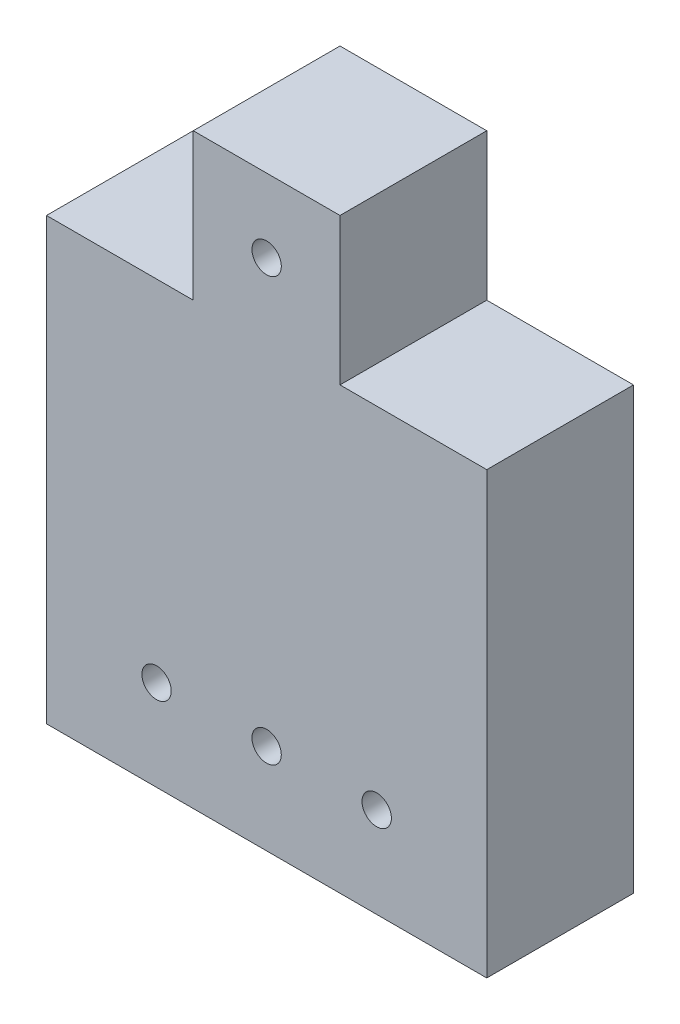
SolidWorks part; units mm, degrees
ref_plane "Front Plane" through (0, 0, 0) normal (0, 0, 1) x (1, 0, 0)
ref_plane "Top Plane" through (0, 0, 0) normal (0, 1, 0) x (1, 0, 0)
ref_plane "Right Plane" through (0, 0, 0) normal (1, 0, 0) x (0, 0, -1)
sketch "Sketch1" plane through (0, 0, 0) normal (0, 0, 1) x (1, 0, 0)
  line L1 (0, 0) -> (19.05, 0)
  line L2 (0, 0) -> (0, 25.4)
  line L3 (0, 25.4) -> (19.05, 25.4)
  line L4 (19.05, 0) -> (19.05, 25.4)
  dimension "D1" = 19.05
  dimension "D2" = 25.4
extrude "Boss-Extrude1" add sketch "Sketch1" along normal blind 6.35
sketch "Sketch2" plane through (0, 0, 0) normal (0, 0, -1) x (-1, 0, 0)
  line L1 (0, 25.4) -> (-6.35, 25.4)
  line L2 (0, 25.4) -> (0, 19.05)
  line L3 (0, 19.05) -> (-6.35, 19.05)
  line L4 (-6.35, 25.4) -> (-6.35, 19.05)
  dimension "D1" = 6.35
  dimension "D2" = 6.35
extrude "Cut-Extrude1" cut sketch "Sketch2" against normal through all
sketch "Sketch3" plane through (0, 0, 0) normal (0, 0, -1) x (-1, 0, 0)
  line L1 (-19.05, 25.4) -> (-12.7, 25.4)
  line L2 (-19.05, 25.4) -> (-19.05, 19.05)
  line L3 (-19.05, 19.05) -> (-12.7, 19.05)
  line L4 (-12.7, 25.4) -> (-12.7, 19.05)
  dimension "D1" = 6.35
  dimension "D2" = 6.35
extrude "Cut-Extrude2" cut sketch "Sketch3" against normal through all
sketch "Sketch4" plane through (0, 0, 0) normal (0, 0, -1) x (-1, 0, 0)
  line L0 (-9.525, 22.225) -> (-9.525, 19.05) construction
  line L1 (-9.525, 22.225) -> (-6.35, 22.225) construction
  line L4 (-6.35, 25.4) -> (-12.7, 25.4)
  line L5 (-12.7, 25.4) -> (-12.7, 19.05)
  line L6 (-12.7, 19.05) -> (-6.35, 19.05)
  line L7 (-6.35, 19.05) -> (-6.35, 25.4)
  line L8 (-6.35, 25.4) -> (-12.7, 25.4) construction
  line L9 (-12.7, 25.4) -> (-12.7, 19.05) construction
  line L10 (-12.7, 19.05) -> (-6.35, 19.05) construction
  line L11 (-6.35, 19.05) -> (-6.35, 25.4) construction
  circle A0 centre (-9.525, 22.225) radius 0.635
  dimension "D2" = 1.27
  dimension "D1" = 0
extrude "Cut-Extrude3" cut sketch "Sketch4" against normal through all
sketch "Sketch5" plane through (0, 0, 6.35) normal (0, 0, 1) x (1, 0, 0)
  line L0 (9.525, 3.9221) -> (14.2875, 3.9221) construction
  line L1 (4.7625, 3.9221) -> (9.525, 3.9221) construction
  line L2 (4.7625, 3.9221) -> (0, 3.9221) construction
  line L3 (0, 19.05) -> (0, 0) construction
  line L4 (14.2875, 3.9221) -> (19.05, 3.9221) construction
  line L5 (19.05, 0) -> (19.05, 19.05) construction
  circle A0 centre (14.2875, 3.9221) radius 0.635
  circle A1 centre (9.525, 3.9221) radius 0.635
  circle A2 centre (4.7625, 3.9221) radius 0.635
  dimension "D1" = 1.27
  dimension "D2" = 4.7625
extrude "Cut-Extrude4" cut sketch "Sketch5" against normal through all
